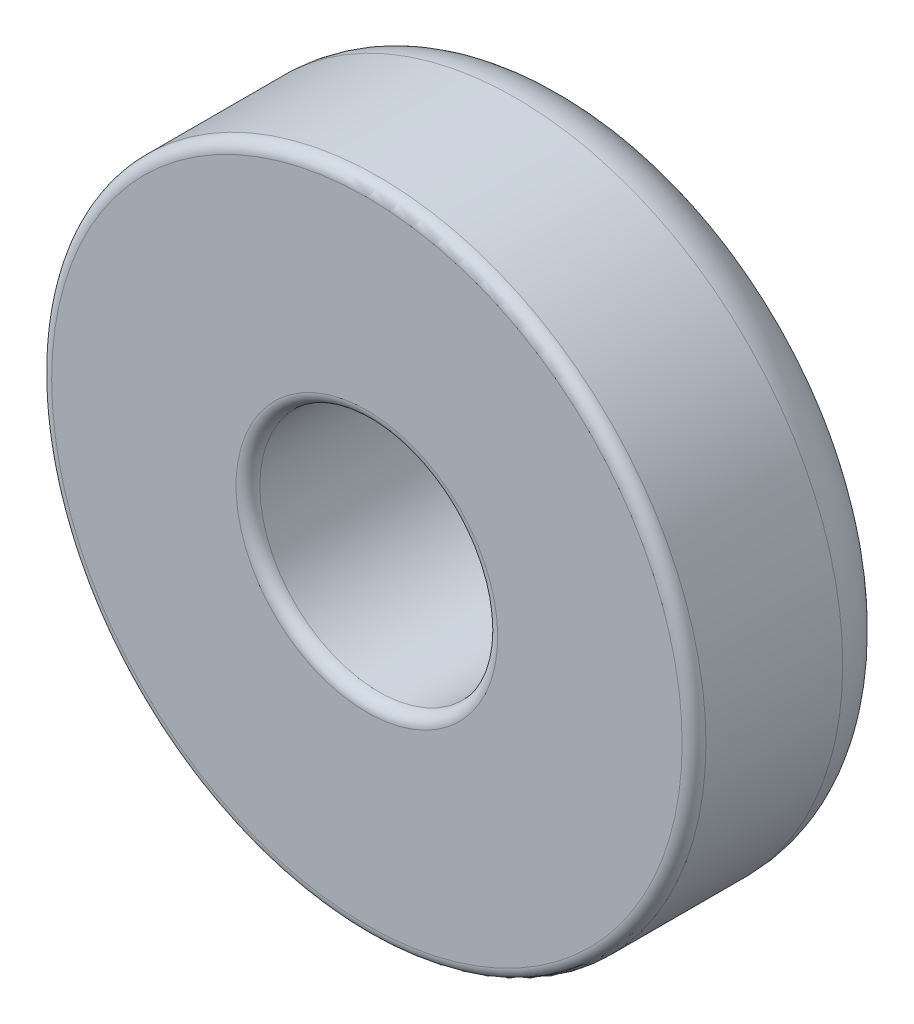
SolidWorks part; units mm, degrees
ref_plane "Front Plane" through (0, 0, 0) normal (0, 0, 1) x (1, 0, 0)
ref_plane "Top Plane" through (0, 0, 0) normal (0, 1, 0) x (1, 0, 0)
ref_plane "Right Plane" through (0, 0, 0) normal (1, 0, 0) x (0, 0, -1)
sketch "Sketch1" plane through (0, 0, 0) normal (0, 0, 1) x (1, 0, 0)
  circle A0 centre (0, 0) radius 1
  dimension "D1" = 2
extrude "Extrude-Thin1" add sketch "Sketch1" along normal blind 1.75 thin
fillet "Fillet1" radius 0.5 1 edges at (2.75, 0, 0)
fillet "Fillet2" radius 0.1 3 edges at (2.75, 0, 1.75) (1, 0, 1.75) (1, 0, 0)
